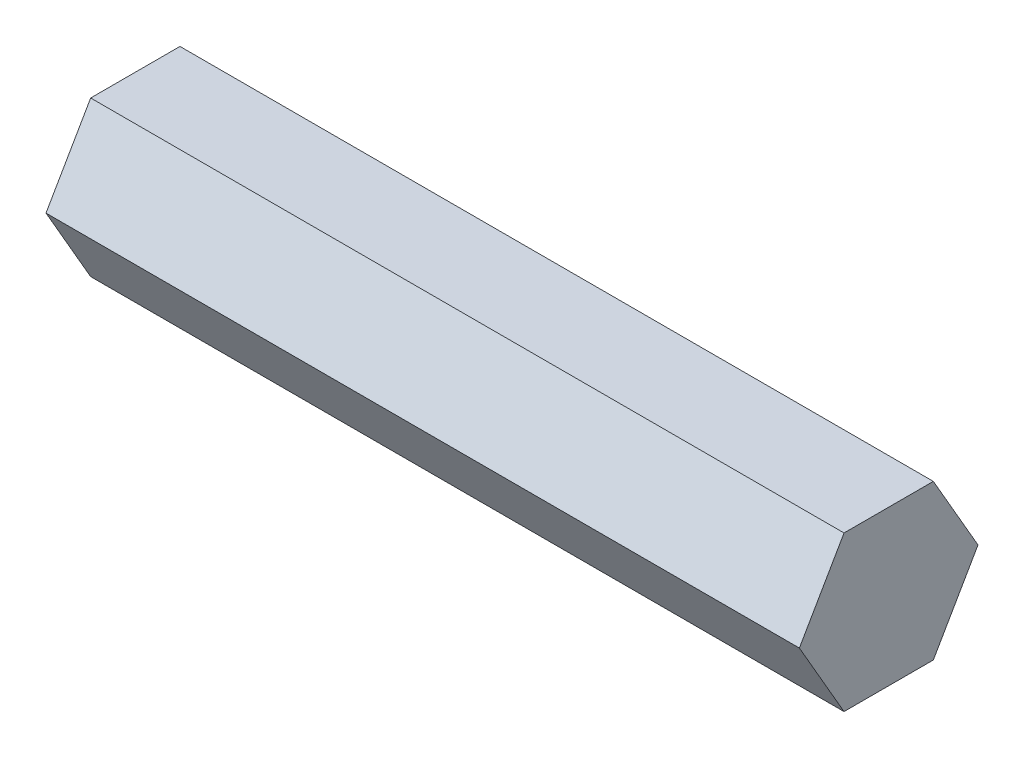
SolidWorks part; units mm, degrees
ref_plane "Front Plane" through (0, 0, 0) normal (0, 0, 1) x (1, 0, 0)
ref_plane "Top Plane" through (0, 0, 0) normal (0, 1, 0) x (1, 0, 0)
ref_plane "Right Plane" through (0, 0, 0) normal (1, 0, 0) x (0, 0, -1)
sketch "Sketch1" plane through (0, 0, 0) normal (1, 0, 0) x (0, 0, -1)
  line L1 (7.3323, 0) -> (3.6662, 6.35)
  line L2 (3.6662, 6.35) -> (-3.6662, 6.35)
  line L3 (-3.6662, 6.35) -> (-7.3323, 0)
  line L4 (-7.3323, 0) -> (-3.6662, -6.35)
  line L5 (-3.6662, -6.35) -> (3.6662, -6.35)
  line L6 (3.6662, -6.35) -> (7.3323, 0)
  circle A0 centre (0, 0) radius 6.35 construction
  dimension "D1" = 12.7
extrude "Boss-Extrude1" add sketch "Sketch1" along normal blind 61.85
